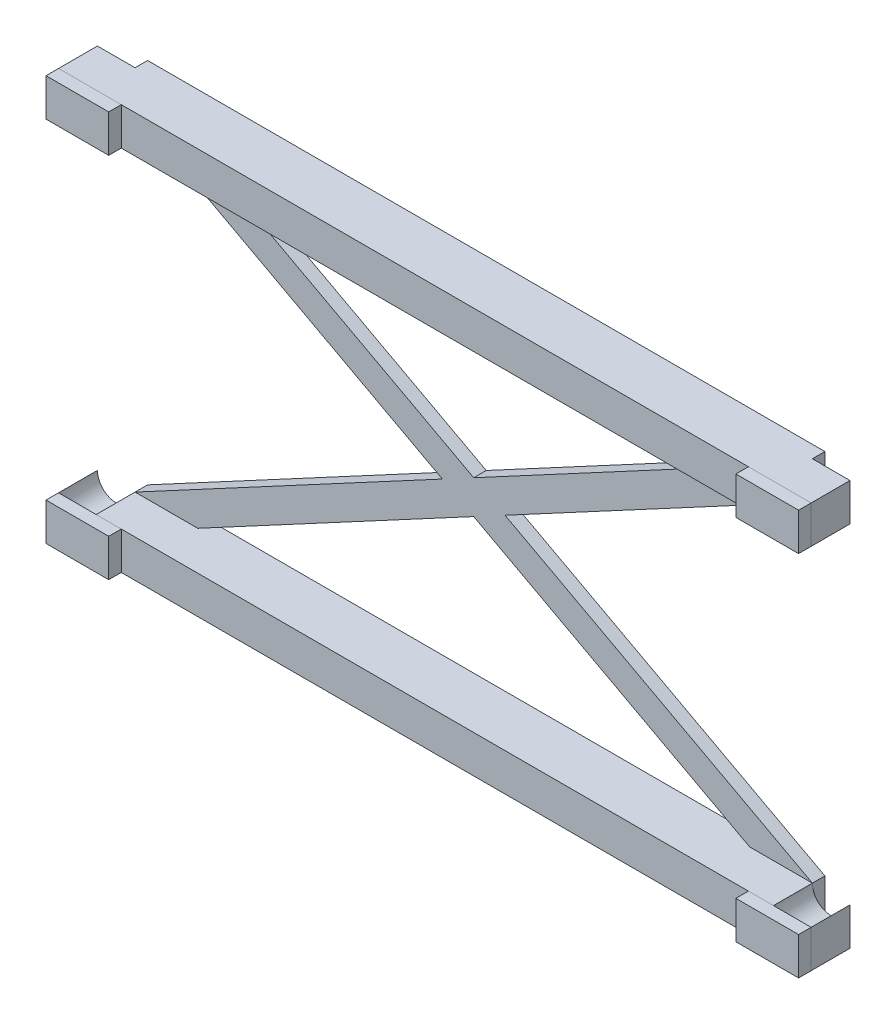
SolidWorks part; units mm, degrees
ref_plane "Front Plane" through (0, 0, 0) normal (0, 0, 1) x (1, 0, 0)
ref_plane "Top Plane" through (0, 0, 0) normal (0, 1, 0) x (1, 0, 0)
ref_plane "Right Plane" through (0, 0, 0) normal (1, 0, 0) x (0, 0, -1)
sketch "male_origin" plane through (0, 0, 0) normal (0, 0, 1) x (1, 0, 0)
  line L0 (10, 0) -> (30, 0)
  line L1 (0, -1000) -> (0, 49000) construction
  line L2 (0, 0) -> (0, 3)
  line L3 (-27, 3) -> (27, 3)
  line L4 (0, 0) -> (0, -20)
  line L5 (-30, -23) -> (-27, -23) construction
  line L6 (30, 3) -> (30, 0)
  line L7 (10, -10) -> (49000, -10) construction
  line L8 (10, 0) -> (10, -20)
  line L9 (0, 0) -> (0, -10) construction
  line L10 (-1000, -10) -> (0, -10) construction
  line L11 (30, -23) -> (27, -23) construction
  line L12 (-10, -20) -> (-30, -20)
  line L13 (30, -23) -> (30, -20)
  line L14 (-27, -23) -> (27, -23)
  line L15 (-30, -23) -> (-30, -20)
  line L16 (0, -20) -> (0, -23)
  line L17 (10, -20) -> (30, -20)
  line L18 (-10, 0) -> (-10, -20)
  line L19 (-30, 3) -> (-30, 0)
  line L20 (-10, 0) -> (-30, 0)
  line L21 (27, 3) -> (30, 3)
  line L22 (-27, 3) -> (-30, 3)
  line L23 (-30, -23) -> (-27, -23)
  line L24 (27, -23) -> (30, -23)
  dimension "D1" = 30
  dimension "D2" = 3
  dimension "D3" = 10
  dimension "D4" = 20
  dimension "D5" = 3
  dimension "D6" = 10
  dimension "D7" = 30
  dimension "D8" = 3
  dimension "D10" = 27
  dimension "D11" = 10
  dimension "D12" = 27
sketch "female_slide" plane through (0, 0, 0) normal (0, 0, 1) x (1, 0, 0)
  line L0 (-27, -23.15) -> (-36.107, -23.15) construction
  line L6 (0, -10) -> (0, 3.15) construction
  line L7 (0, 0) -> (0, -20) construction
  line L8 (10, -10) -> (249000, -10) construction
  line L9 (-201000, -10) -> (0, -10) construction
  line L10 (0, -10) -> (0, -23.15) construction
  line L14 (-27, 3.15) -> (-28.5, 3.15) construction
  line L15 (-27, 3.15) -> (27, 3.15)
  line L16 (-30, 3.15) -> (-30, 6.15)
  line L17 (27, -23.15) -> (28.5, -23.15) construction
  line L18 (-27, -23.15) -> (27, -23.15)
  line L21 (-30, 6.15) -> (30, 6.15)
  line L26 (30, 6.15) -> (30, 3.15)
  line L27 (-30, -23.15) -> (-30, -26.15)
  line L28 (-30, -26.15) -> (30, -26.15)
  line L29 (30, -26.15) -> (30, -23.15)
  arc A0 (-30, 3.15) -> (-27, 3.15) centre (-28.5, 3.15) cw
  arc A1 (27, 3.15) -> (30, 3.15) centre (28.5, 3.15) cw
  arc A2 (27, -23.15) -> (30, -23.15) centre (28.5, -23.15) ccw
  arc A3 (-30, -23.15) -> (-27, -23.15) centre (-28.5, -23.15) ccw
  dimension "D2" = 3
  dimension "D3" = 3
  dimension "D1" = 13.15
  dimension "D4" = 13.15
  dimension "D5" = 60
sketch "X_back" plane through (0, 0, 0) normal (0, 0, 1) x (1, 0, 0)
  line L0 (22, 6.15) -> (-22, 6.15)
  line L1 (22, 3.15) -> (-22, 3.15)
  line L2 (-2.5, -10) -> (-27, -23.15)
  line L3 (2.6405, -10) -> (49000, -10) construction
  line L4 (22, -23.15) -> (-22, -23.15)
  line L5 (0, -11.3418) -> (-22, -23.15)
  line L6 (2.5, -10) -> (27, -23.15)
  line L7 (0, -11.3418) -> (22, -23.15)
  line L8 (-27, 3.15) -> (-2.5, -10)
  line L9 (-22, 3.15) -> (0, -8.6582)
  line L10 (22, -26.15) -> (-22, -26.15)
  line L11 (22, 3.15) -> (0, -8.6582)
  line L12 (27, 3.15) -> (2.5, -10)
  line L13 (-27, 3.15) -> (-27, 6.15)
  line L14 (-30, 6.15) -> (30, 6.15) construction
  line L15 (-27, 6.15) -> (-22, 6.15)
  line L17 (-1000, -10) -> (-2.5, -10) construction
  line L18 (0, -1010) -> (0, -11.3418) construction
  line L20 (27, 3.15) -> (27, 6.15)
  line L21 (27, 6.15) -> (22, 6.15)
  line L22 (27, -23.15) -> (27, -26.15)
  line L23 (27, -26.15) -> (22, -26.15)
  line L26 (-27, -26.15) -> (-22, -26.15)
  line L27 (-27, -23.15) -> (-27, -26.15)
  dimension "D1" = 5
  dimension "D2" = 3
  dimension "D3" = 27.806
  dimension "D5" = 5
extrude "Boss-Extrude1" add sketch "female_slide" along normal blind 3.1
extrude "Boss-Extrude2" add sketch "X_back" against normal blind 1 contours L20 L21 L0 L15 L13 L8 L2 L27 L26 L10 L23 L22 L6 L12
sketch "Sketch1" plane through (0, 0, 0) normal (0, 0, 1) x (1, 0, 0)
  line L0 (22, 3.15) -> (-22, 3.15) construction
  line L1 (22, 3.15) -> (0, -8.6582) construction
  line L2 (-22, 3.15) -> (0, -8.6582) construction
  line L3 (0, -11.3418) -> (-22, -23.15) construction
  line L4 (0, -11.3418) -> (22, -23.15) construction
  line L5 (22, -23.15) -> (-22, -23.15) construction
  line L6 (22, 3.15) -> (-22, 3.15)
  line L7 (22, 3.15) -> (0, -8.6582)
  line L8 (-22, 3.15) -> (0, -8.6582)
  line L9 (0, -11.3418) -> (-22, -23.15)
  line L10 (0, -11.3418) -> (22, -23.15)
  line L11 (22, -23.15) -> (-22, -23.15)
extrude "Cut-Extrude1" cut sketch "Sketch1" against normal through all
sketch "Sketch2" plane through (0, 0, 3.1) normal (0, 0, 1) x (1, 0, 0)
  line L0 (30, 3.15) -> (30, 6.15)
  line L1 (30, 6.15) -> (25, 6.15)
  line L2 (30, 6.15) -> (-30, 6.15) construction
  line L3 (25, 6.15) -> (25, 3.15)
  line L4 (25, 3.15) -> (30, 3.15)
  line L5 (0, 6.15) -> (0, 3.15) construction
  line L6 (-27, 3.15) -> (27, 3.15) construction
  line L7 (-30, 3.15) -> (-30, 6.15)
  line L8 (-30, 6.15) -> (-25, 6.15)
  line L9 (-25, 6.15) -> (-25, 3.15)
  line L10 (-25, 3.15) -> (-30, 3.15)
  line L11 (0, 3.15) -> (0, -23.15) construction
  line L12 (27, -23.15) -> (-27, -23.15) construction
  line L13 (-1000, -10) -> (49000, -10) construction
  line L14 (25, -23.15) -> (30, -23.15)
  line L15 (30, -23.15) -> (30, -26.15)
  line L16 (30, -26.15) -> (25, -26.15)
  line L17 (25, -26.15) -> (25, -23.15)
  line L18 (-25, -23.15) -> (-30, -23.15)
  line L19 (-30, -23.15) -> (-30, -26.15)
  line L20 (-30, -26.15) -> (-25, -26.15)
  line L21 (-25, -26.15) -> (-25, -23.15)
  point P22 (0, -10)
  dimension "D1" = 5
extrude "Boss-Extrude3" add sketch "Sketch2" along normal blind 1 separate body
